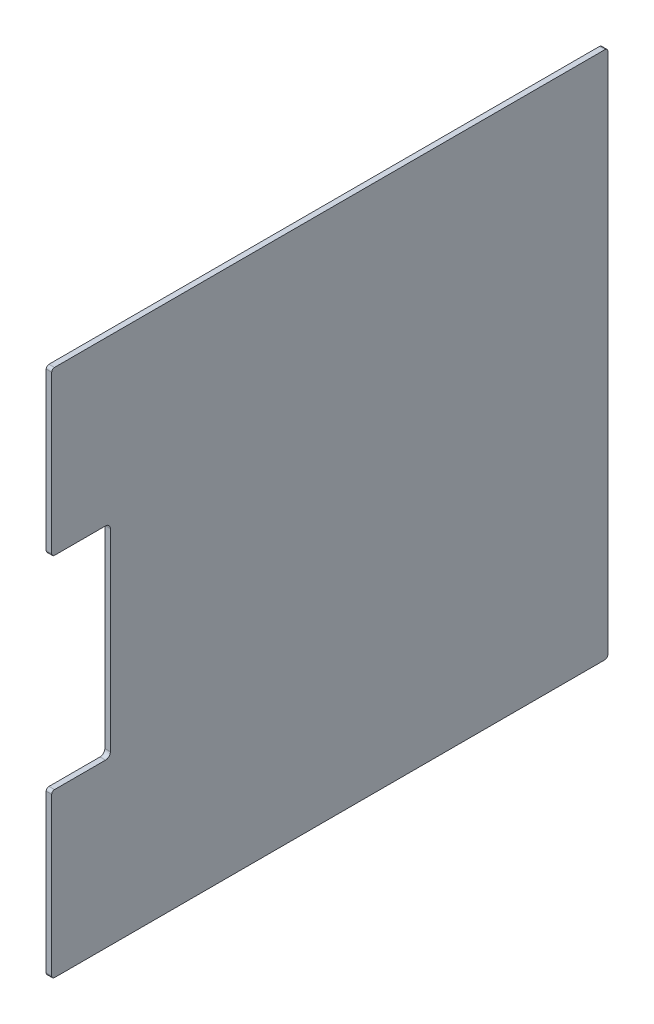
SolidWorks part; units mm, degrees
ref_plane "Front Plane" through (0, 0, 0) normal (0, 0, 1) x (1, 0, 0)
ref_plane "Top Plane" through (0, 0, 0) normal (0, 1, 0) x (1, 0, 0)
ref_plane "Right Plane" through (0, 0, 0) normal (1, 0, 0) x (0, 0, -1)
ref_plane "Plane1" through (-22.4932, 0, 0) normal (1, 0, 0) x (0, 0, -1)
sketch "Sketch1" plane through (-22.4932, 0, 0) normal (1, 0, 0) x (0, 0, -1)
  line L0 (41.5, -352.5226) -> (41.5, 26.4774)
  line L1 (39.5, 28.4774) -> (-359.5, 28.4774)
  line L2 (-361.5, 26.4774) -> (-361.5, -87.4997)
  line L3 (-359.5, -89.4997) -> (-322.5, -89.4997)
  line L4 (-319, -92.9997) -> (-319, -232.9997)
  line L5 (-322.5, -236.4997) -> (-359.5, -236.4997)
  line L6 (-361.5, -238.4997) -> (-361.5, -352.5226)
  line L7 (-359.5, -354.5226) -> (39.5, -354.5226)
  arc A0 (39.5, -354.5226) -> (41.5, -352.5226) centre (39.5, -352.5226) ccw
  arc A1 (41.5, 26.4774) -> (39.5, 28.4774) centre (39.5, 26.4774) ccw
  arc A2 (-359.5, 28.4774) -> (-361.5, 26.4774) centre (-359.5, 26.4774) ccw
  arc A3 (-361.5, -87.4997) -> (-359.5, -89.4997) centre (-359.5, -87.4997) ccw
  arc A4 (-322.5, -89.4997) -> (-319, -92.9997) centre (-322.5, -92.9997) cw
  arc A5 (-319, -232.9997) -> (-322.5, -236.4997) centre (-322.5, -232.9997) cw
  arc A6 (-359.5, -236.4997) -> (-361.5, -238.4997) centre (-359.5, -238.4997) ccw
  arc A7 (-361.5, -352.5226) -> (-359.5, -354.5226) centre (-359.5, -352.5226) ccw
extrude "Boss-Extrude1" add sketch "Sketch1" against normal blind 4
